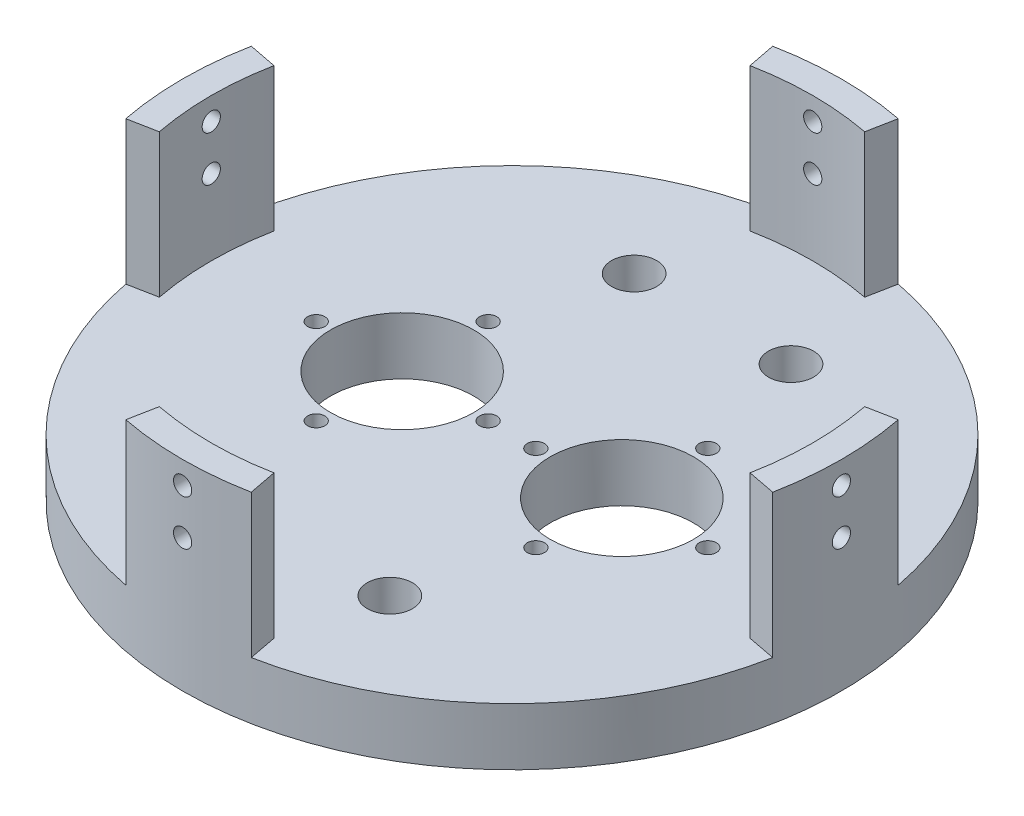
SolidWorks part; units mm, degrees
material "AISI 1020"
ref_plane "Front Plane" through (0, 0, 0) normal (0, 0, 1) x (1, 0, 0)
ref_plane "Top Plane" through (0, 0, 0) normal (0, 1, 0) x (1, 0, 0)
ref_plane "Right Plane" through (0, 0, 0) normal (1, 0, 0) x (0, 0, -1)
ref_axis "Longitudinal Axis" through (0, 0, 0) along (0, 1, 0)
sketch "Sketch1" plane through (0, 0, 0) normal (0, 1, 0) x (1, 0, 0)
  circle A0 centre (0, 0) radius 73.025
  dimension "D1" = 146.05
extrude "Base Extrude" add sketch "Sketch1" along normal blind 12.7
sketch "Sketch2" plane through (0, 12.7, 0) normal (0, 1, 0) x (1, 0, 0)
  line L0 (0, 0) -> (-64.256, 12.4675)
  line L1 (0, 0) -> (-64.256, -12.4675)
  line L2 (-64.256, -12.4675) -> (-66.675, 0) construction
  line L3 (-64.256, 12.4675) -> (-66.675, 0) construction
  line L4 (-66.675, 0) -> (0, 0) construction
  line L5 (-65.4543, 12.7) -> (-71.688, 13.9095)
  line L6 (-65.4543, -12.7) -> (-71.688, -13.9095)
  line L7 (-64.256, 12.4675) -> (-65.4543, 12.7) construction
  line L8 (-65.4543, -12.7) -> (-64.256, -12.4675) construction
  circle A0 centre (0, 0) radius 73.025 construction
  arc A1 (-71.688, 13.9095) -> (-71.688, -13.9095) centre (0, 0) ccw
  arc A2 (-65.4543, 12.7) -> (-65.4543, -12.7) centre (0, 0) ccw
  point P14 (-66.675, 0)
  circle M4 centre (0, 0) radius 73.025
  dimension "D1" = 6.35
  dimension "D2" = 25.4
extrude "Standoffs" add sketch "Sketch2" along normal blind 31.75 contours A2 L5 L6 M4
ref_plane "Plane1" through (-73.025, 0, 0) normal (-1, 0, 0) x (0, 0, 1)
sketch "Hole Positions" plane through (-73.025, 0, 0) normal (-1, 0, 0) x (0, 0, 1)
  line L0 (0, 44.45) -> (0, 0) construction
  line L1 (13.9095, 44.45) -> (-13.9095, 44.45) construction
  point P5 (0, 39.45)
  point P6 (0, 29.45)
  dimension "D1" = 5
  dimension "D2" = 10
pattern_circular "CirPattern1" count 4 over 360 about axis through (0, 0, 0) along (0, 1, 0) of "Standoffs"
hole_wizard "#10-32 Tapped Hole1" positions "Sketch6" profile "Sketch7" tap size "#10-32" standard "ANSI Inch"
sketch "Sketch6" plane through (-73.025, 0, 0) normal (-1, 0, 0) x (0, 0, 1)
  point P0 (0, 39.45)
  point P3 (0, 29.45)
cosmetic thread "Hole Thread1" parameters "D1"=9.652, "D2"=4.826
cosmetic thread "Hole Thread2" parameters "D1"=9.652, "D2"=4.826
sketch "Sketch7" plane through (-73.025, 39.45, 0) normal (0, 1, 0) x (0, 0, 1)
  line L0 (0, 0) -> (0, 26.6133)
  line L1 (0, 26.6133) -> (2.0193, 25.4)
  line L2 (2.0193, 25.4) -> (2.0193, 0)
  line L5 (2.0193, 0) -> (0, 0)
  line L10 (0, 26.6133) -> (-2.0193, 25.4) construction
  line L11 (0, -6.35) -> (0, 107.95) construction
  dimension "Tap Drill Dia." = 4.0386
  dimension "Tap Drill Depth" = 25.4
  dimension "Drill Angle" = 118
pattern_circular "CirPattern2" count 4 over 360 about axis through (0, 0, 0) along (0, 1, 0) of "#10-32 Tapped Hole1"
cosmetic thread "Hole Thread9" parameters "D1"=9.652, "D2"=4.826
cosmetic thread "Hole Thread10" parameters "D1"=9.652, "D2"=4.826
cosmetic thread "Hole Thread11" parameters "D1"=9.652, "D2"=4.826
cosmetic thread "Hole Thread12" parameters "D1"=9.652, "D2"=4.826
cosmetic thread "Hole Thread13" parameters "D1"=9.652, "D2"=4.826
cosmetic thread "Hole Thread14" parameters "D1"=9.652, "D2"=4.826
sketch "Sketch3" plane through (0, 12.7, 0) normal (0, 1, 0) x (1, 0, 0)
  line L0 (24.3421, 0) -> (-24.3421, 0) construction
  line L1 (0, 0) -> (0, 73.025) construction
  line L2 (-24.3421, -19.05) -> (-24.3421, 19.05) construction
  line L3 (-17.38, -44.45) -> (-57.9383, -44.45) construction
  line L5 (-24.3421, 0) -> (-43.3921, 0) construction
  line L6 (24.3421, 0) -> (43.3921, 0) construction
  line L7 (24.3421, -19.05) -> (24.3421, 19.05) construction
  circle A0 centre (-24.3421, 0) radius 15.875
  arc A1 (71.688, 13.9095) -> (13.9095, 71.688) centre (0, 0) ccw construction
  circle A2 centre (24.3421, 0) radius 15.875
  circle A3 centre (-24.3421, 19.05) radius 1.905
  circle A4 centre (-24.3421, -19.05) radius 1.905
  circle A11 centre (-17.38, -44.45) radius 5
  arc A12 (-71.688, -13.9095) -> (-13.9095, -71.688) centre (0, 0) ccw construction
  circle A13 centre (17.3799, -44.45) radius 5
  circle A14 centre (17.3799, 44.45) radius 5
  circle A15 centre (-17.38, 44.45) radius 5
  circle A16 centre (-43.3921, 0) radius 1.905
  circle A17 centre (-5.2921, 0) radius 1.905
  circle A18 centre (24.3421, -19.05) radius 1.905
  circle A19 centre (43.3921, 0) radius 1.905
  circle A20 centre (5.2921, 0) radius 1.905
  circle A21 centre (24.3421, 19.05) radius 1.905
  point P21 (-24.3421, 0)
  dimension "D1" = 31.75
  dimension "D3" = 3.81
  dimension "D6" = 10
  dimension "D2" = 48.6842
  dimension "D4" = 38.1
  dimension "D7" = 88.9
  dimension "D9" = 38.1
  dimension "D5" = 19.05
  dimension "D10" = 34.7599
extrude "Body-Holes" cut sketch "Sketch3" along direction (0, 1, 0) on the side against the normal up to surface (12.7 mm away)
